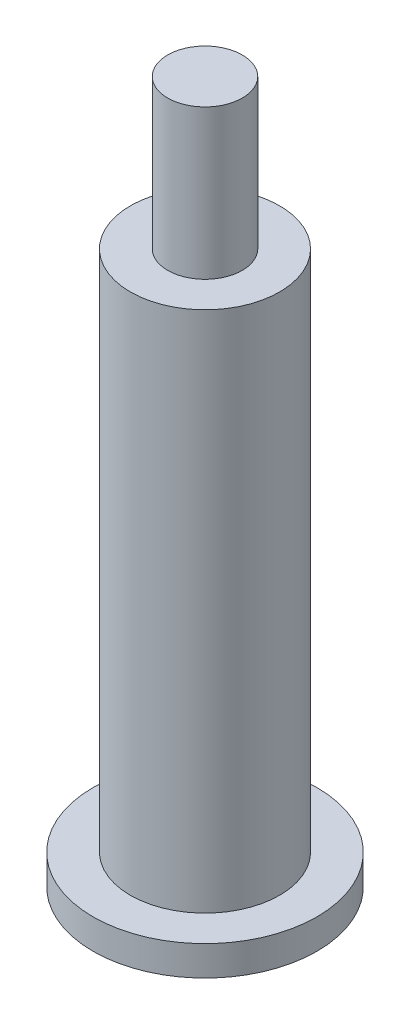
SolidWorks part; units mm, degrees
ref_plane "Alzado" through (0, 0, 0) normal (0, 0, 1) x (1, 0, 0)
ref_plane "Planta" through (0, 0, 0) normal (0, 1, 0) x (1, 0, 0)
ref_plane "Vista lateral" through (0, 0, 0) normal (1, 0, 0) x (0, 0, -1)
sketch "Croquis1" plane through (0, 0, 0) normal (0, 1, 0) x (1, 0, 0)
  circle A0 centre (0, 0) radius 9.525
  dimension "0.75" = 19.05
extrude "Saliente-Extruir1" add sketch "Croquis1" along normal blind 2.54
sketch "Croquis2" plane through (0, 2.54, 0) normal (0, 1, 0) x (1, 0, 0)
  circle A0 centre (0, 0) radius 6.35
  dimension "D1" = 12.7
extrude "Saliente-Extruir2" add sketch "Croquis2" along normal blind 44.45
sketch "Croquis5" plane through (0, 46.99, 0) normal (0, 1, 0) x (1, 0, 0)
  circle A0 centre (0, 0) radius 3.175
  dimension "D1" = 6.35
extrude "Saliente-Extruir4" add sketch "Croquis5" along normal blind 12.7
